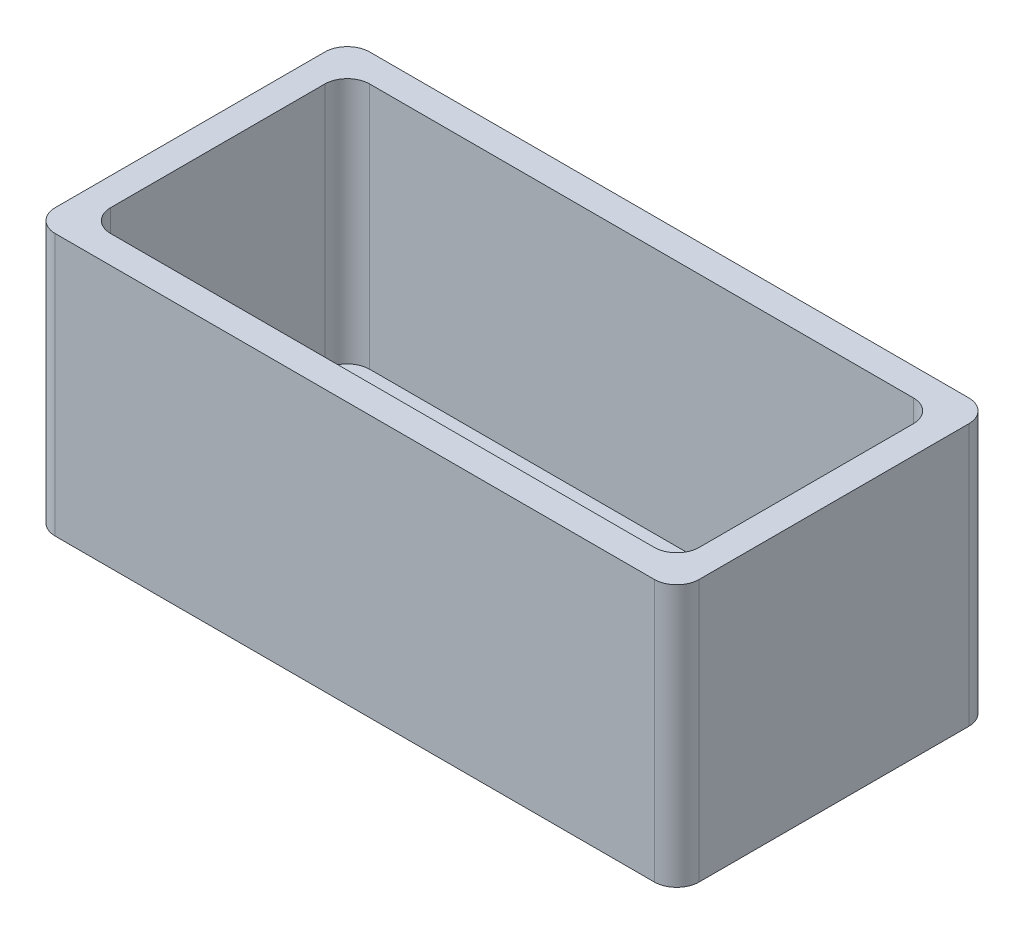
SolidWorks part; units mm, degrees
ref_plane "Front Plane" through (0, 0, 0) normal (0, 0, 1) x (1, 0, 0)
ref_plane "Top Plane" through (0, 0, 0) normal (0, 1, 0) x (1, 0, 0)
ref_plane "Right Plane" through (0, 0, 0) normal (1, 0, 0) x (0, 0, -1)
sketch "Sketch1" plane through (0, 0, 0) normal (0, 1, 0) x (1, 0, 0)
  line L0 (77, 10) -> (86, 10) construction
  line L1 (0, 0) -> (86, 0)
  line L2 (0, 0) -> (0, 42)
  line L3 (0, 42) -> (86, 42)
  line L4 (86, 0) -> (86, 42)
  line L5 (9, 10) -> (0, 10) construction
  circle A0 centre (9, 10) radius 1.5
  circle A1 centre (77, 10) radius 1.5
  point P8 (55.7159, 2.325)
  dimension "D2" = 3
  dimension "D1" = 68
  dimension "D3" = 10
  dimension "D4" = 42
  dimension "D5" = 9
  dimension "D6" = 86
extrude "Boss-Extrude1" add sketch "Sketch1" along normal blind 35
fillet "Fillet1" radius 3 4 edges at (86, 17.5, 0) (86, 17.5, -42) (0, 17.5, -42) (0, 17.5, 0)
sketch "Sketch2" plane through (0, 35, 0) normal (0, 1, 0) x (1, 0, 0)
  line L24 (3.7, 3.7) -> (82.3, 3.7)
  line L25 (82.3, 3.7) -> (82.3, 38.3)
  line L26 (82.3, 38.3) -> (3.7, 38.3)
  line L27 (3.7, 38.3) -> (3.7, 3.7)
  line L28 (6.7, 3.7) -> (79.3, 3.7)
  line L29 (82.3, 6.7) -> (82.3, 35.3)
  line L30 (79.3, 38.3) -> (6.7, 38.3)
  line L31 (3.7, 35.3) -> (3.7, 6.7)
  arc A19 (6.7, 38.3) -> (3.7, 35.3) centre (6.7, 35.3) ccw
  arc A20 (6.7, 3.7) -> (3.7, 6.7) centre (6.7, 6.7) cw
  arc A21 (79.3, 3.7) -> (82.3, 6.7) centre (79.3, 6.7) ccw
  arc A22 (82.3, 35.3) -> (79.3, 38.3) centre (79.3, 35.3) ccw
  dimension "D2" = 3
  dimension "D1" = 3.7
extrude "Cut-Extrude1" cut sketch "Sketch2" against normal offset from surface (33 mm away) 2 up to face at (9, 0, -8.5)
